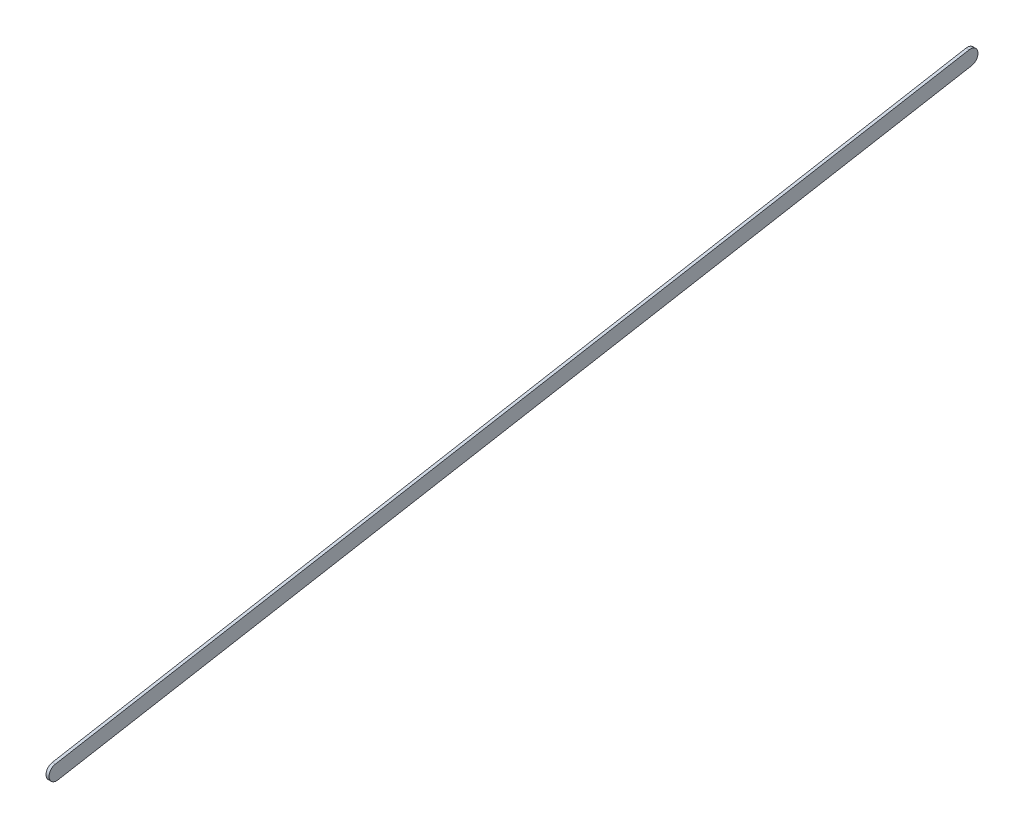
SolidWorks part; units mm, degrees
ref_plane "Front Plane" through (0, 0, 0) normal (0, 0, 1) x (1, 0, 0)
ref_plane "Top Plane" through (0, 0, 0) normal (0, 1, 0) x (1, 0, 0)
ref_plane "Right Plane" through (0, 0, 0) normal (1, 0, 0) x (0, 0, -1)
sketch "Sketch1" plane through (0, 0, 0) normal (1, 0, 0) x (0, 0, -1)
  line L0 (0, 0) -> (-900.9966, -159.4684) construction
  line L1 (0, 0) -> (-900.9966, -159.4684) construction
  line L2 (1.3071, -7.3852) -> (-899.6895, -166.8536)
  line L3 (-1.3071, 7.3852) -> (-902.3037, -152.0832)
  arc A0 (1.3071, -7.3852) -> (-1.3071, 7.3852) centre (0, 0) ccw
  arc A1 (-902.3037, -152.0832) -> (-899.6895, -166.8536) centre (-900.9966, -159.4684) ccw
  point P3 (-450.4983, -79.7342)
  dimension "D2" = 7.5
  dimension "D1" = 915
extrude "Boss-Extrude1" add sketch "Sketch1" along normal blind 3
